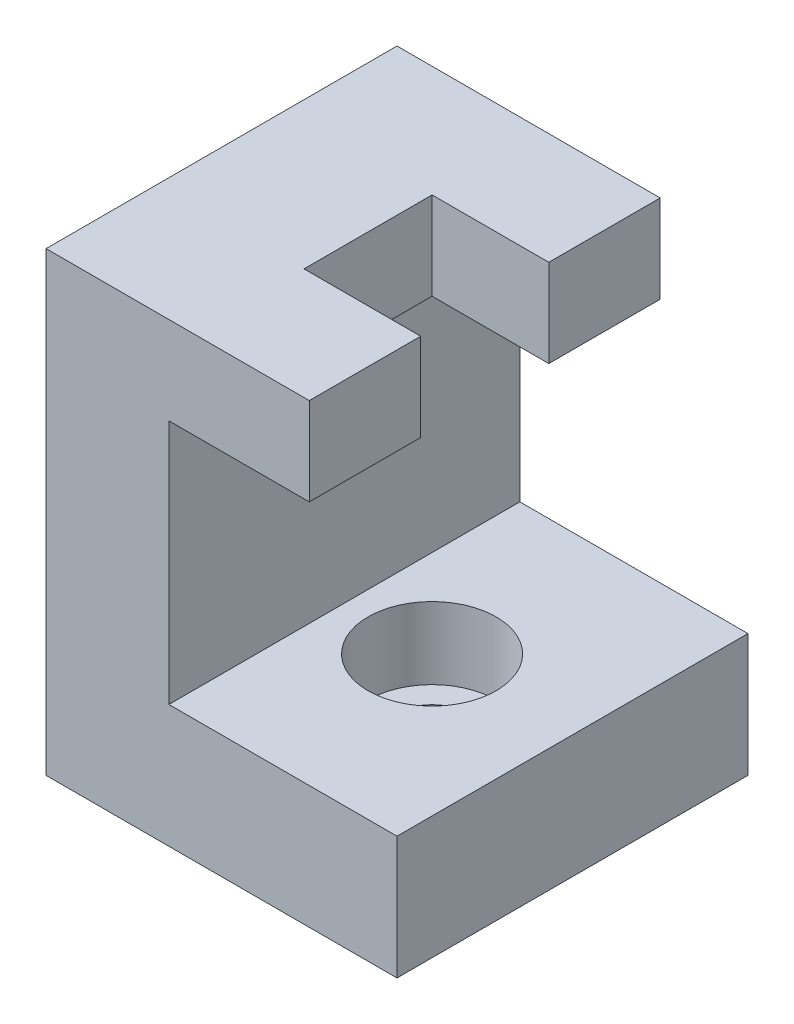
SolidWorks part; units mm, degrees
ref_plane "前基準面" through (0, 0, 0) normal (0, 0, 1) x (1, 0, 0)
ref_plane "上基準面" through (0, 0, 0) normal (0, 1, 0) x (1, 0, 0)
ref_plane "右基準面" through (0, 0, 0) normal (1, 0, 0) x (0, 0, -1)
sketch "草圖1" plane through (0, 0, 0) normal (0, 0, 1) x (1, 0, 0)
  line L3 (0, 0) -> (20, 0)
  line L4 (0, 0) -> (0, 7)
  line L5 (0, 7) -> (20, 7)
  line L6 (20, 0) -> (20, 7)
  line L8 (0, 7) -> (0, 21)
  line L10 (7, 7) -> (7, 21)
  line L11 (0, 21) -> (15, 21)
  line L12 (0, 21) -> (0, 26)
  line L13 (0, 26) -> (15, 26)
  line L14 (15, 21) -> (15, 26)
  dimension "D1" = 20
  dimension "D2" = 7
  dimension "D3" = 5
  dimension "D4" = 7
  dimension "D5" = 14
  dimension "D6" = 15
extrude "填料-伸長1" add sketch "草圖1" along normal mid plane 20
sketch "草圖2" plane through (0, 7, 0) normal (0, 1, 0) x (1, 0, 0)
  line L0 (-11, 0) -> (11, 0) construction
  line L1 (0, -11) -> (0, 11) construction
  circle A0 centre (12, 0) radius 3.65
  dimension "D1" = 7.3
  dimension "D2" = 12
extrude "除料-伸長1" cut sketch "草圖2" against normal blind 4.1
sketch "草圖4" plane through (0, 26, 0) normal (0, 1, 0) x (1, 0, 0)
  line L1 (8.35, 3.65) -> (15.65, 3.65)
  line L2 (8.35, 3.65) -> (8.35, -3.65)
  line L3 (8.35, -3.65) -> (15.65, -3.65)
  line L4 (15.65, 3.65) -> (15.65, -3.65)
  line L5 (8.35, 3.65) -> (15.65, -3.65) construction
  line L6 (8.35, -3.65) -> (15.65, 3.65) construction
  circle A0 centre (12, 0) radius 3.65 construction
  point P0 (12, 0)
extrude "除料-伸長3" cut sketch "草圖4" against normal up to next contours L2 L1 L4 L3
sketch "草圖3" plane through (0, 2.9, 0) normal (0, 1, 0) x (1, 0, 0)
  circle A0 centre (12, 0) radius 2.25
  dimension "D1" = 4.5
extrude "除料-伸長2" cut sketch "草圖3" against normal up to next
